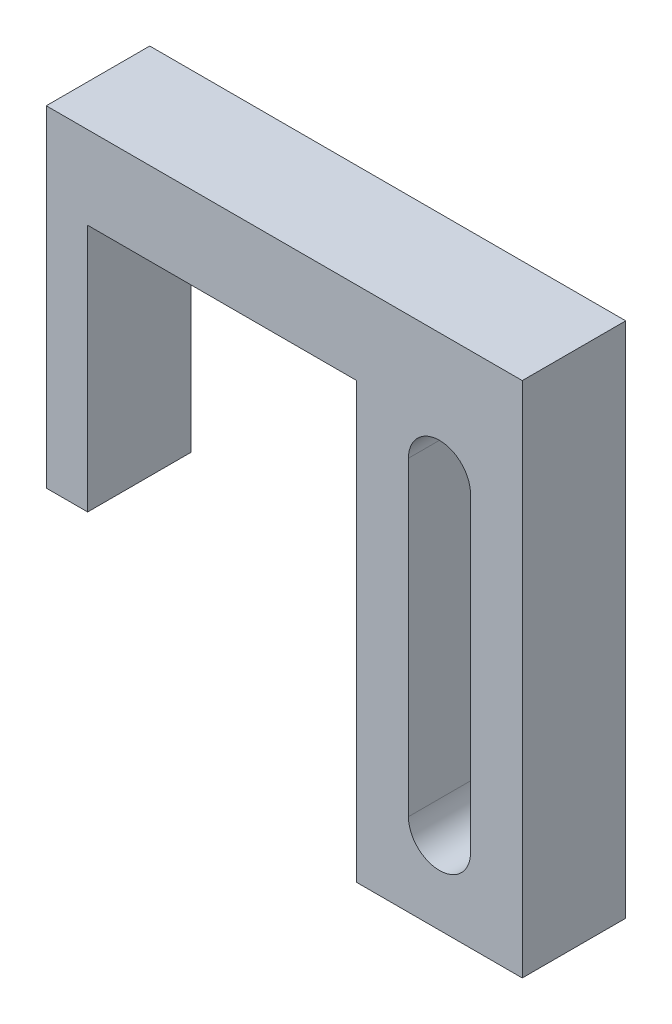
SolidWorks part; units mm, degrees
ref_plane "Front Plane" through (0, 0, 0) normal (0, 0, 1) x (1, 0, 0)
ref_plane "Top Plane" through (0, 0, 0) normal (0, 1, 0) x (1, 0, 0)
ref_plane "Right Plane" through (0, 0, 0) normal (1, 0, 0) x (0, 0, -1)
sketch "Sketch1" plane through (0, 0, 0) normal (0, 0, 1) x (1, 0, 0)
  line L1 (4, -12.5) -> (-4, -12.5)
  line L2 (4, -12.5) -> (4, 12.5)
  line L3 (4, 12.5) -> (-4, 12.5)
  line L4 (-4, -12.5) -> (-4, 12.5)
  line L5 (4, -12.5) -> (-4, 12.5) construction
  line L6 (4, 12.5) -> (-4, -12.5) construction
  point P0 (0, 0)
  dimension "D1" = 8
  dimension "D2" = 25
extrude "Boss-Extrude6" add sketch "Sketch1" along normal mid plane 5 contours L3 L4 L1 L2
sketch "Sketch7" plane through (-4, 0, 0) normal (-1, 0, 0) x (0, 0, 1)
sketch "Sketch8" plane through (0, 0, 2.5) normal (0, 0, 1) x (1, 0, 0)
  line L0 (-4, 12.5) -> (-19, 12.5)
  line L1 (-4, 12.5) -> (-4, 8.5)
  line L2 (-19, 12.5) -> (-19, 8.5)
  line L3 (-4, 8.5) -> (-19, 8.5)
  dimension "D1" = 4
  dimension "D2" = 15
extrude "Boss-Extrude7" add sketch "Sketch8" against normal up to surface (5 mm away) up to face at (0, 0, -2.5)
sketch "Sketch9" plane through (0, 8.5, 0) normal (0, -1, 0) x (1, 0, 0)
  line L0 (-19, 2.5) -> (-19, -2.5)
  line L1 (-19, 2.5) -> (-17, 2.5)
  line L2 (-19, -2.5) -> (-17, -2.5)
  line L3 (-17, 2.5) -> (-17, -2.5)
  dimension "D1" = 2
extrude "Boss-Extrude8" add sketch "Sketch9" along normal blind 12
sketch "Sketch10" plane through (0, 0, 2.5) normal (0, 0, 1) x (1, 0, 0)
  line L0 (0, 6.5) -> (0, -8.5) construction
  line L1 (1.5, 6.5) -> (1.5, -8.5)
  line L2 (-1.5, 6.5) -> (-1.5, -8.5)
  line L3 (4, -12.5) -> (-4, -12.5) construction
  line L4 (4, 12.5) -> (-19, 12.5) construction
  arc A0 (1.5, 6.5) -> (-1.5, 6.5) centre (0, 6.5) ccw
  arc A1 (-1.5, -8.5) -> (1.5, -8.5) centre (0, -8.5) ccw
  point P3 (0, -1)
  dimension "D1" = 1.5
  dimension "D2" = 4
  dimension "D3" = 6
extrude "Cut-Extrude1" cut sketch "Sketch10" against normal through all
